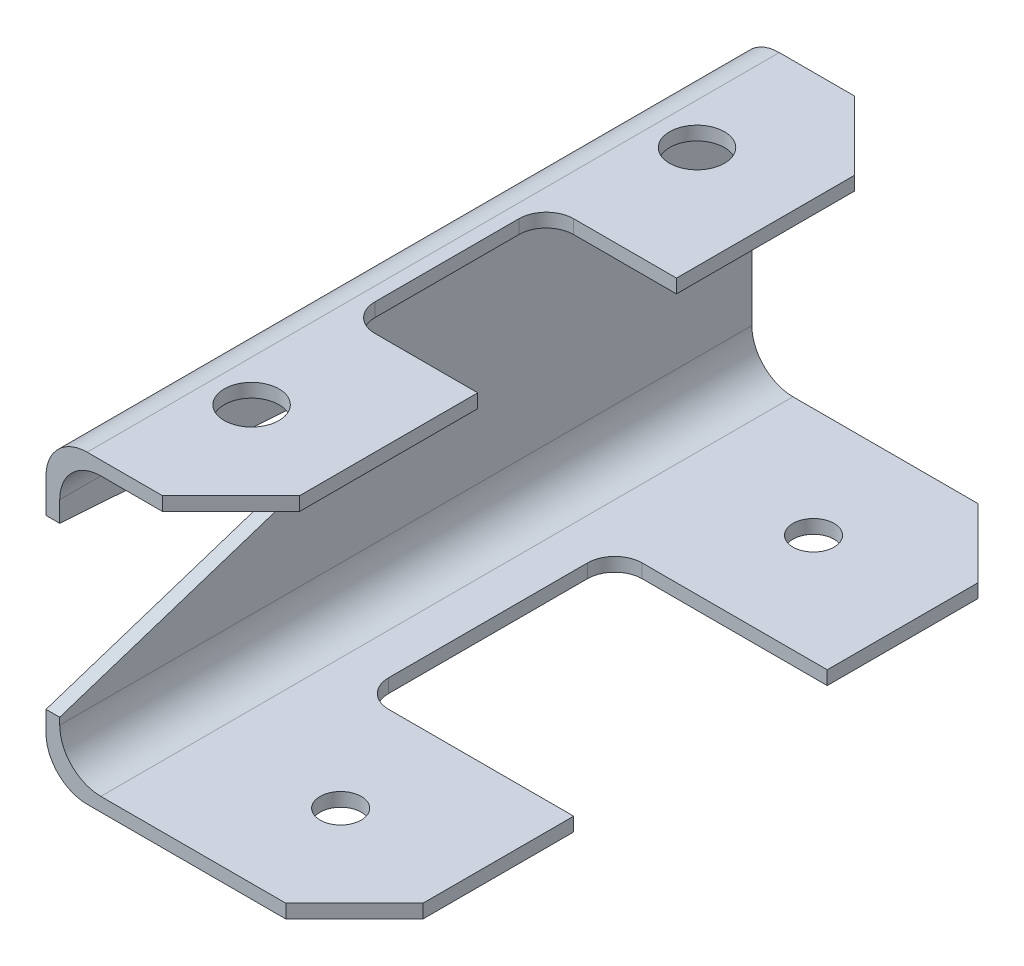
SolidWorks part; units mm, degrees
ref_plane "Front Plane" through (0, 0, 0) normal (0, 0, 1) x (1, 0, 0)
ref_plane "Top Plane" through (0, 0, 0) normal (0, 1, 0) x (1, 0, 0)
ref_plane "Right Plane" through (0, 0, 0) normal (1, 0, 0) x (0, 0, -1)
sketch "Sketch1" plane through (0, 0, 0) normal (0, 0, 1) x (1, 0, 0)
  line L0 (0, 0) -> (-61.9125, 0)
  line L1 (-71.4375, 9.525) -> (-71.4375, 61.1187)
  line L2 (-61.9125, 70.6437) -> (-28.575, 70.6437)
  line L3 (-28.575, 70.6437) -> (-28.575, 67.4688)
  line L4 (-28.575, 67.4688) -> (-58.7375, 67.4688)
  line L5 (-68.2625, 57.9437) -> (-68.2625, 12.7)
  line L6 (-58.7375, 3.175) -> (0, 3.175)
  line L7 (0, 3.175) -> (0, 0)
  arc A0 (-58.7375, 67.4688) -> (-68.2625, 57.9437) centre (-58.7375, 57.9437) ccw
  arc A1 (-71.4375, 61.1187) -> (-61.9125, 70.6437) centre (-61.9125, 61.1187) cw
  arc A2 (-68.2625, 12.7) -> (-58.7375, 3.175) centre (-58.7375, 12.7) ccw
  arc A3 (-61.9125, 0) -> (-71.4375, 9.525) centre (-61.9125, 9.525) cw
  point P13 (-71.4375, 70.6437)
  point P18 (-71.4375, 0)
  dimension "D7" = 9.525
  dimension "D1" = 71.4375
  dimension "D2" = 70.6437
  dimension "D3" = 42.8625
  dimension "D4" = 3.175
  dimension "D5" = 3.175
  dimension "D6" = 3.175
extrude "Boss-Extrude1" add sketch "Sketch1" along normal mid plane 160.3375
sketch "Sketch2" plane through (-68.2625, 0, 0) normal (1, 0, 0) x (0, 0, -1)
  line L0 (-80.1688, 53.1812) -> (-22.4715, 49.1936)
  line L1 (-80.1688, 12.7) -> (-80.1688, 57.9437) construction
  line L2 (0, 57.9437) -> (0, 12.7) construction
  line L3 (-80.1688, 57.9437) -> (80.1688, 57.9437) construction
  line L4 (-80.1688, 12.7) -> (80.1688, 12.7) construction
  line L6 (-80.1688, 53.1812) -> (-80.1688, 14.2875)
  line L7 (-80.1688, 0) -> (80.1688, 0) construction
  line L9 (-80.1688, 14.2875) -> (-20.5576, 33.7287)
  line L10 (-80.1688, 70.6437) -> (80.1688, 70.6437) construction
  circle A0 centre (-23.0187, 41.275) radius 7.9375
  line M9 (-80.1688, 57.9437) -> (-80.1688, 12.7)
  dimension "D3" = 15.875
  dimension "D1" = 17.4625
  dimension "D2" = 14.2875
  dimension "D5" = 57.15
  dimension "D6" = 41.275
extrude "Cut-Extrude2" cut sketch "Sketch2" against normal through all contours A0 L0 L9 M9 | A0 L9
sketch "Sketch3" plane through (0, 70.6437, 0) normal (0, 1, 0) x (1, 0, 0)
  line L0 (-44.45, 80.1688) -> (-28.575, 64.2938)
  line L1 (-28.575, 80.1688) -> (-61.9125, 80.1688) construction
  line L2 (-28.575, -80.1688) -> (-28.575, 80.1688) construction
  line L3 (-44.45, 80.1688) -> (-28.575, 80.1688)
  line L4 (-28.575, 80.1688) -> (-28.575, 64.2938)
  line L5 (-61.9125, 0) -> (0, 0) construction
  line L6 (-61.9125, -80.1688) -> (-61.9125, 80.1688) construction
  line L7 (-28.575, -80.1688) -> (-28.575, -64.2938)
  line L8 (-44.45, -80.1688) -> (-28.575, -80.1688)
  line L9 (-44.45, -80.1688) -> (-28.575, -64.2938)
  line L10 (-15.875, 80.1688) -> (0, 64.2938)
  line L11 (0, 80.1688) -> (0, 64.2938)
  line L12 (-15.875, 80.1688) -> (0, 80.1688)
  line L13 (0, -80.1688) -> (0, 80.1688) construction
  line L14 (0, 80.1688) -> (-58.7375, 80.1688) construction
  line L15 (-15.875, -80.1688) -> (0, -80.1688)
  line L16 (0, -80.1688) -> (0, -64.2938)
  line L17 (-15.875, -80.1688) -> (0, -64.2938)
  line L18 (-28.575, 23.0187) -> (-28.575, -23.0188)
  line L19 (-28.575, -23.0188) -> (-52.3875, -23.0188)
  line L20 (-58.7375, -16.6688) -> (-58.7375, 16.6687)
  line L21 (-52.3875, 23.0188) -> (-28.575, 23.0187)
  arc A0 (-52.3875, -23.0188) -> (-58.7375, -16.6688) centre (-52.3875, -16.6688) cw
  arc A1 (-58.7375, 16.6687) -> (-52.3875, 23.0188) centre (-52.3875, 16.6687) cw
  circle A2 centre (-52.3875, 51.5938) radius 6.35
  circle A3 centre (-52.3875, -51.5937) radius 6.35
  point P32 (-58.7375, -23.0188)
  dimension "D8" = 6.35
  dimension "D9" = 12.7
  dimension "D1" = 45
  dimension "D2" = 15.875
  dimension "D3" = 15.875
  dimension "D4" = 45
  dimension "D5" = 46.0375
  dimension "D6" = 57.15
  dimension "D7" = 30.1625
  dimension "D10" = 103.1875
  dimension "D11" = 28.575
  dimension "D12" = 23.8125
extrude "Cut-Extrude3" cut sketch "Sketch3" against normal up to next
sketch "Sketch4" plane through (0, 3.175, 0) normal (0, 1, 0) x (1, 0, 0)
  line L0 (0, -64.2938) -> (0, 64.2938) construction
  line L1 (-15.875, 80.1688) -> (-58.7375, 80.1688) construction
  line L2 (-15.875, -80.1688) -> (-58.7375, -80.1688) construction
  line L3 (0, 29.3687) -> (-42.8625, 29.3687)
  line L4 (0, 29.3687) -> (0, -29.3687)
  line L5 (0, -29.3687) -> (-42.8625, -29.3688)
  line L6 (-49.2125, 23.0187) -> (-49.2125, -23.0187)
  circle A0 centre (-28.575, 54.7688) radius 4.7625
  circle A1 centre (-28.575, -54.7687) radius 4.7625
  arc A2 (-42.8625, -29.3688) -> (-49.2125, -23.0187) centre (-42.8625, -23.0188) cw
  arc A3 (-42.8625, 29.3687) -> (-49.2125, 23.0187) centre (-42.8625, 23.0187) ccw
  point P18 (-49.2125, 29.3687)
  dimension "D1" = 9.525
  dimension "D8" = 6.35
  dimension "D2" = 28.575
  dimension "D3" = 109.5375
  dimension "D4" = 25.4
  dimension "D5" = 49.2125
  dimension "D6" = 58.7375
  dimension "D7" = 50.8
extrude "Cut-Extrude4" cut sketch "Sketch4" against normal up to next
